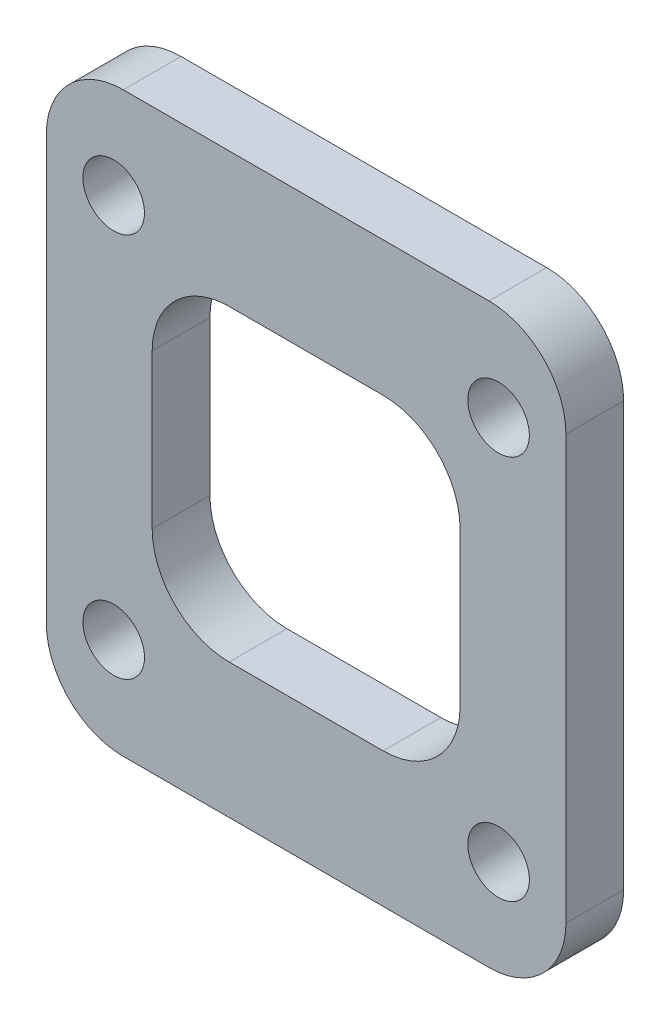
SolidWorks part; units mm, degrees
material "A-玻璃纤维"
ref_plane "前视基准面" through (0, 0, 0) normal (0, 0, 1) x (1, 0, 0)
ref_plane "上视基准面" through (0, 0, 0) normal (0, 1, 0) x (1, 0, 0)
ref_plane "右视基准面" through (0, 0, 0) normal (1, 0, 0) x (0, 0, -1)
sketch "草图1" plane through (0, 0, 0) normal (0, 0, 1) x (1, 0, 0)
  line L0 (0, 19.0624) -> (0, -19.9366) construction
  line L1 (-10, -10) -> (10, -10) construction
  line L2 (-10, -10) -> (-10, 10) construction
  line L3 (-10, 10) -> (10, 10) construction
  line L4 (10, -10) -> (10, 10) construction
  line L5 (-10, -10) -> (10, 10) construction
  line L6 (-10, 10) -> (10, -10) construction
  line L7 (21.3797, 0) -> (-19.2824, 0) construction
  line L9 (-13.5, -15) -> (13.5, -15)
  line L10 (-13.5, -15) -> (-13.5, 15)
  line L11 (-13.5, 15) -> (13.5, 15)
  line L12 (13.5, -15) -> (13.5, 15)
  line L13 (-13.5, -15) -> (13.5, 15) construction
  line L14 (-13.5, 15) -> (13.5, -15) construction
  circle A0 centre (10, 10) radius 1.6
  circle A1 centre (10, -10) radius 1.6
  circle A2 centre (-10, -10) radius 1.6
  circle A3 centre (-10, 10) radius 1.6
  point P0 (0, 0)
  point P14 (0, 0)
  dimension "D1" = 20
  dimension "D2" = 3.2
  dimension "D3" = 30
  dimension "D4" = 27
extrude "凸台-拉伸1" add sketch "草图1" along normal blind 3
sketch "草图2" plane through (0, 0, 3) normal (0, 0, 1) x (1, 0, 0)
  line L1 (-8, -8) -> (8, -8)
  line L2 (-8, -8) -> (-8, 8)
  line L3 (-8, 8) -> (8, 8)
  line L4 (8, -8) -> (8, 8)
  line L5 (-8, -8) -> (8, 8) construction
  line L6 (-8, 8) -> (8, -8) construction
  point P0 (0, 0)
  dimension "D1" = 16
  dimension "D2" = 16
extrude "切除-拉伸1" cut sketch "草图2" against normal through all
fillet "圆角1" radius 4 8 edges at (-13.5, -15, 1.5) (13.5, -15, 1.5) (13.5, 15, 1.5) (-13.5, 15, 1.5) (8, -8, 1.5) (-8, -8, 1.5) (8, 8, 1.5) (-8, 8, 1.5)
